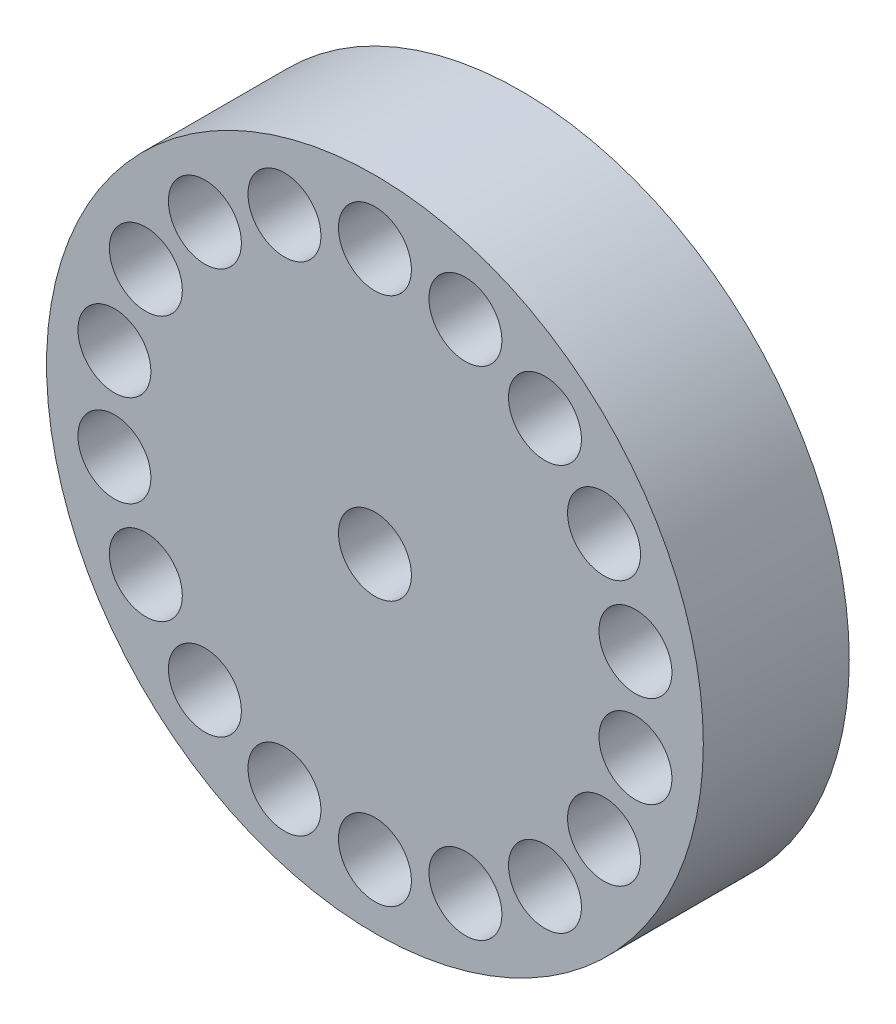
SolidWorks part; units mm, degrees
ref_plane "Płaszczyzna przednia" through (0, 0, 0) normal (0, 0, 1) x (1, 0, 0)
ref_plane "Płaszczyzna górna" through (0, 0, 0) normal (0, 1, 0) x (1, 0, 0)
ref_plane "Płaszczyzna prawa" through (0, 0, 0) normal (1, 0, 0) x (0, 0, -1)
sketch "Szkic1" plane through (0, 0, 0) normal (0, 0, 1) x (1, 0, 0)
  circle A0 centre (0, 0) radius 4.5
  circle A1 centre (0, 0) radius 0.5
extrude "Dodanie-wyciągnięcie1" add sketch "Szkic1" along normal blind 2
sketch "Szkic2" plane through (0, 0, 2) normal (0, 0, 1) x (1, 0, 0)
  circle A0 centre (0, 3.625) radius 0.5
  circle A1 centre (1.2398, 3.4064) radius 0.5
  circle A2 centre (2.3301, 2.7769) radius 0.5
  circle A3 centre (3.1393, 1.8125) radius 0.5
  circle A4 centre (3.5699, 0.6295) radius 0.5
  circle A5 centre (3.5699, -0.6295) radius 0.5
  circle A6 centre (3.1393, -1.8125) radius 0.5
  circle A7 centre (2.3301, -2.7769) radius 0.5
  circle A8 centre (1.2398, -3.4064) radius 0.5
  circle A9 centre (0, -3.625) radius 0.5
  circle A10 centre (-1.2398, -3.4064) radius 0.5
  circle A11 centre (-2.3301, -2.7769) radius 0.5
  circle A12 centre (-3.1393, -1.8125) radius 0.5
  circle A13 centre (-3.5699, -0.6295) radius 0.5
  circle A14 centre (-3.5699, 0.6295) radius 0.5
  circle A15 centre (-3.1393, 1.8125) radius 0.5
  circle A16 centre (-2.3301, 2.7769) radius 0.5
  circle A17 centre (-1.2398, 3.4064) radius 0.5
  point P40 (0, 0)
  dimension "D1" = 1
  dimension "D2" = 3.625
  dimension "D3" = 18
extrude "Wytnij-wyciągnięcie2" cut sketch "Szkic2" against normal blind 1
